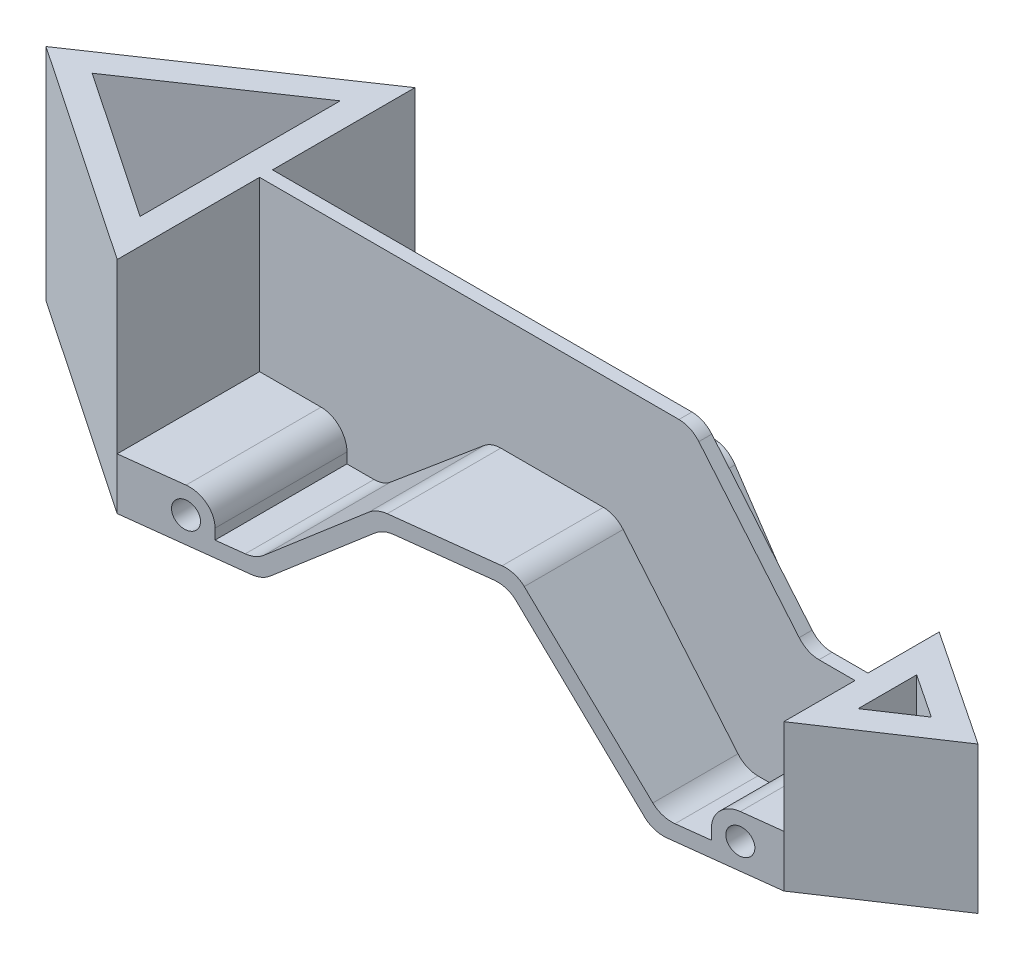
SolidWorks part; units mm, degrees
material "1060 Alloy"
ref_plane "Front Plane" through (0, 0, 0) normal (0, 0, 1) x (1, 0, 0)
ref_plane "Top Plane" through (0, 0, 0) normal (0, 1, 0) x (1, 0, 0)
ref_plane "Right Plane" through (0, 0, 0) normal (1, 0, 0) x (0, 0, -1)
sketch "Sketch2" plane through (0, 0, 0) normal (0, 1, 0) x (1, 0, 0)
  line L0 (0, -57.5) -> (0, 57.5)
  line L1 (0, 57.5) -> (-85, 0)
  line L2 (-85, 0) -> (0, -57.5)
  line L3 (-10, 38.6621) -> (-67.1527, 0)
  line L4 (-67.1527, 0) -> (-10, -38.6621)
  line L5 (-10, -38.6621) -> (-10, 38.6621)
  point P4 (0, 0)
  dimension "D1" = 57.5
  dimension "D2" = 85
  dimension "D3" = 10
extrude "Boss-Extrude1" add sketch "Sketch2" along normal blind 85
sketch "Sketch3" plane through (0, 0, 0) normal (0, 0, 1) x (1, 0, 0)
  line L0 (0, 0) -> (50, 0)
  line L1 (50, 0) -> (91.7114, 35)
  line L2 (91.7114, 35) -> (134.654, 35)
  line L3 (134.654, 35) -> (185, -25)
  line L4 (185, -25) -> (230, -25)
  line L6 (47.8162, 6) -> (89.5276, 41)
  line L7 (89.5276, 41) -> (137.4519, 41)
  line L8 (137.4519, 41) -> (187.7978, -19)
  line L9 (187.7978, -19) -> (205, -19)
  line L10 (0, 20) -> (0, 0)
  line L11 (230, -19) -> (230, -25)
  line L12 (0, 20) -> (23.75, 20)
  line L13 (0, 85) -> (0, 0) construction
  line L14 (33.75, 10) -> (33.75, 6)
  line L15 (33.75, 6) -> (47.8162, 6)
  line L16 (0, 6) -> (47.8162, 6) construction
  line L17 (215, -5) -> (230, -5)
  line L18 (230, -5) -> (230, -19)
  line L19 (205, -15) -> (205, -19)
  line L20 (187.7978, -19) -> (230, -19) construction
  circle A0 centre (23.75, 10) radius 5
  arc A1 (33.75, 10) -> (23.75, 20) centre (23.75, 10) ccw
  circle A2 centre (215, -15) radius 5
  arc A3 (215, -5) -> (205, -15) centre (215, -15) ccw
  dimension "D11" = 10
  dimension "D15" = 10
  dimension "D1" = 50
  dimension "D2" = 35
  dimension "D3" = 60
  dimension "D4" = 45
  dimension "D5" = 140
  dimension "D6" = 130
  dimension "D7" = 230
  dimension "D9" = 23.75
  dimension "D10" = 10
  dimension "D12" = 10
  dimension "D13" = 6
  dimension "D14" = 20
  dimension "D16" = 10
  dimension "D17" = 15
  dimension "D18" = 10
  dimension "D19" = 20
  dimension "D8" = 6
extrude "Boss-Extrude2" add sketch "Sketch3" along normal mid plane 115
sketch "Sketch4" plane through (0, 0, 0) normal (0, 1, 0) x (1, 0, 0)
  line L0 (230, -30) -> (230, 30)
  line L1 (230, -57.5) -> (230, 57.5) construction
  line L2 (230, 30) -> (275, 0)
  line L3 (275, 0) -> (230, -30)
  line L4 (240, 11.3148) -> (256.9722, 0)
  line L5 (256.9722, 0) -> (240, -11.3148)
  line L6 (240, -11.3148) -> (240, 11.3148)
  point P5 (230, 0)
  dimension "D1" = 30
  dimension "D2" = 45
  dimension "D3" = 10
extrude "Boss-Extrude3" add sketch "Sketch4" along normal blind 56.6667 from surface at -25 starting at face at (207.5, -25, 0)
sketch "Sketch5" plane through (0, 0, 0) normal (0, 0, 1) x (1, 0, 0)
  line L0 (0, 85) -> (166.6721, 85)
  line L1 (166.6721, 85) -> (211.4241, 31.6667)
  line L2 (211.4241, 31.6667) -> (230, 31.6667)
  line L3 (134.654, 35) -> (185, -25) construction
  line L4 (0, 85) -> (0, 20)
  line L5 (230, 31.6667) -> (230, -5) construction
  line L6 (230, -5) -> (215, -5) construction
  line L7 (205, -19) -> (187.7978, -19) construction
  line L8 (187.7978, -19) -> (137.4519, 41) construction
  line L9 (137.4519, 41) -> (89.5276, 41) construction
  line L10 (89.5276, 41) -> (47.8162, 6) construction
  line L11 (47.8162, 6) -> (33.75, 6) construction
  line L12 (33.75, 6) -> (33.75, 10) construction
  line L13 (23.75, 20) -> (0, 20) construction
  line L14 (230, 31.6667) -> (230, -5)
  line L15 (230, -5) -> (215, -5)
  line L16 (205, -19) -> (187.7978, -19)
  line L17 (187.7978, -19) -> (137.4519, 41)
  line L18 (137.4519, 41) -> (89.5276, 41)
  line L19 (89.5276, 41) -> (47.8162, 6)
  line L20 (47.8162, 6) -> (33.75, 6)
  line L21 (33.75, 6) -> (33.75, 10)
  line L22 (23.75, 20) -> (0, 20)
  line L23 (205, -15) -> (205, -19) construction
  line L24 (205, -15) -> (205, -19)
  arc A0 (215, -5) -> (205, -15) centre (215, -15) ccw construction
  arc A1 (33.75, 10) -> (23.75, 20) centre (23.75, 10) ccw construction
  arc A2 (215, -5) -> (205, -15) centre (215, -15) ccw
  arc A3 (33.75, 10) -> (23.75, 20) centre (23.75, 10) ccw
  dimension "D1" = 56.6667
extrude "Boss-Extrude4" add sketch "Sketch5" along normal mid plane 5
fillet "Fillet2" radius 10 14 edges at (47.8162, 6, -30) (89.5276, 41, -30) (187.7978, -19, -30) (137.4519, 41, -30) (185, -25, 0) (134.654, 35, 0) (91.7114, 35, 0) (50, 0, 0) (211.4241, 31.6667, 0) (166.6721, 85, 0) (187.7978, -19, 30) (47.8162, 6, 30) (137.4519, 41, 30) (89.5276, 41, 30)
sketch "Sketch6" plane through (0, 0, 0) normal (0, 1, 0) x (1, 0, 0)
  line L0 (0, 57.5) -> (230, 57.5)
  line L1 (230, 57.5) -> (230, 30)
  line L2 (230, 30) -> (0, 57.5)
  line L3 (0, -57.5) -> (230, -30)
  line L4 (230, -30) -> (230, -57.5)
  line L5 (230, -57.5) -> (0, -57.5)
extrude "Cut-Extrude1" cut sketch "Sketch6" against normal through all both and the other way through all
equation "\"A\" = 230"
equation "\"B\"= 85"
equation "\"D1@Sketch2\"=\"A\"/4"
equation "\"D2@Sketch2\"=\"B\""
equation "\"D1@Boss-Extrude1\"=\"B\""
equation "\"D7@Sketch3\"=\"A\""
equation "\"D1@Boss-Extrude2\"=\"A\"/2"
equation "\"D1@Boss-Extrude3\"=\"B\"*2/3"
equation "\"D1@Boss-Extrude4\"=\"A\"/2"
equation "\"Z\"= ( \"A\" / 8 ) - 5"
equation "\"X\"= \"A\" / 4"
equation "\"Y\"= ( 2 * \"B\" ) / 3"
equation "\"D9@Sketch3\"= \"Z\""
equation "\"D1@Sketch5\"=\"Y\""
